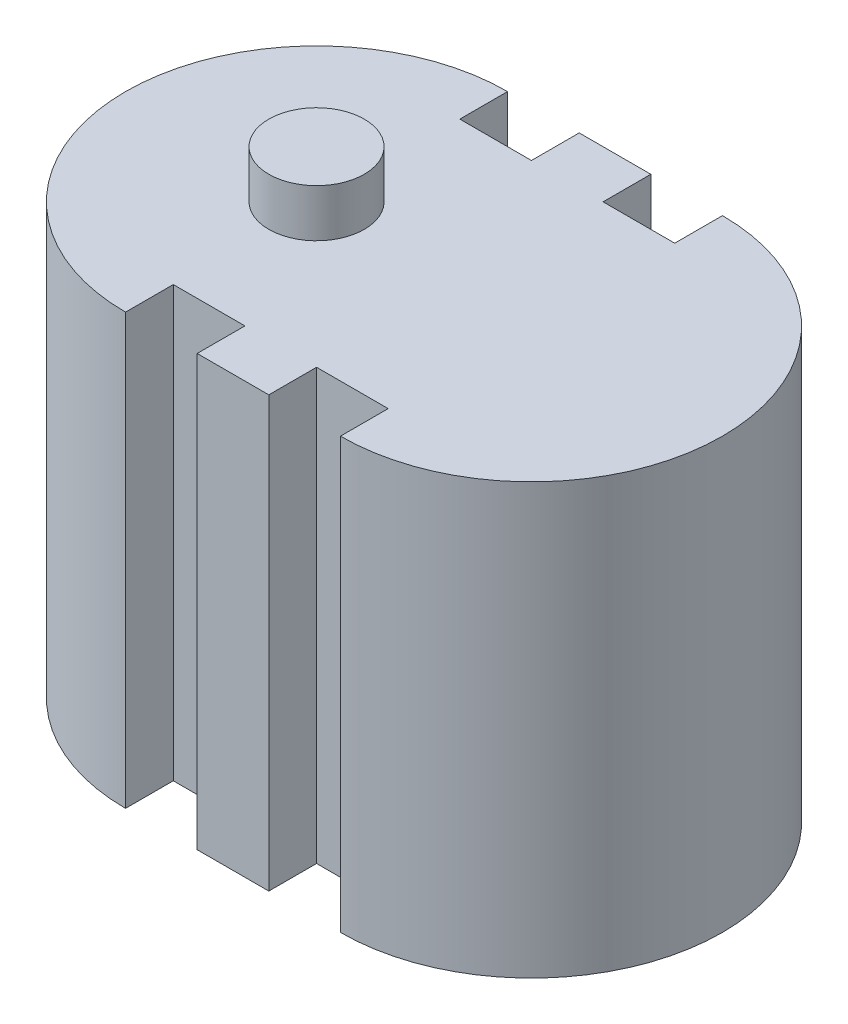
SolidWorks part; units mm, degrees
ref_plane "Front" through (0, 0, 0) normal (0, 0, 1) x (1, 0, 0)
ref_plane "Top" through (0, 0, 0) normal (0, 1, 0) x (1, 0, 0)
ref_plane "Right" through (0, 0, 0) normal (1, 0, 0) x (0, 0, -1)
sketch "Sketch1" plane through (0, 0, 0) normal (0, 1, 0) x (1, 0, 0)
  line L0 (0, 40) -> (0, 30)
  line L1 (15, 40) -> (30, 40)
  line L2 (30, -40) -> (15, -40)
  line L3 (45, 40) -> (45, 30)
  line L4 (15, 40) -> (15, 30)
  line L5 (0, 30) -> (15, 30)
  line L6 (30, 40) -> (30, 30)
  line L7 (45, -30) -> (30, -30)
  line L8 (0, 40) -> (45, 40) construction
  line L9 (45, -40) -> (0, -40) construction
  line L10 (30, -30) -> (30, -40)
  line L11 (30, 40) -> (30, -40) construction
  line L12 (15, -30) -> (0, -30)
  line L13 (45, -30) -> (0, -30) construction
  line L14 (15, -30) -> (15, -40)
  line L15 (15, 40) -> (15, -40) construction
  line L16 (0, -30) -> (0, -40)
  line L17 (0, 40) -> (0, -40) construction
  line L18 (45, -30) -> (45, -40)
  line L19 (45, 40) -> (45, -40) construction
  line L20 (30, 30) -> (45, 30)
  line L21 (0, 30) -> (45, 30) construction
  arc A0 (45, -40) -> (45, 40) centre (45, 0) ccw
  arc A1 (0, 40) -> (0, -40) centre (0, 0) ccw
extrude "Extrude1" add sketch "Sketch1" along normal blind 90
sketch "Sketch2" plane through (0, 90, 0) normal (0, 1, 0) x (-1, 0, 0)
  circle A0 centre (0, 0) radius 10
extrude "Extrude2" add sketch "Sketch2" along normal blind 10
